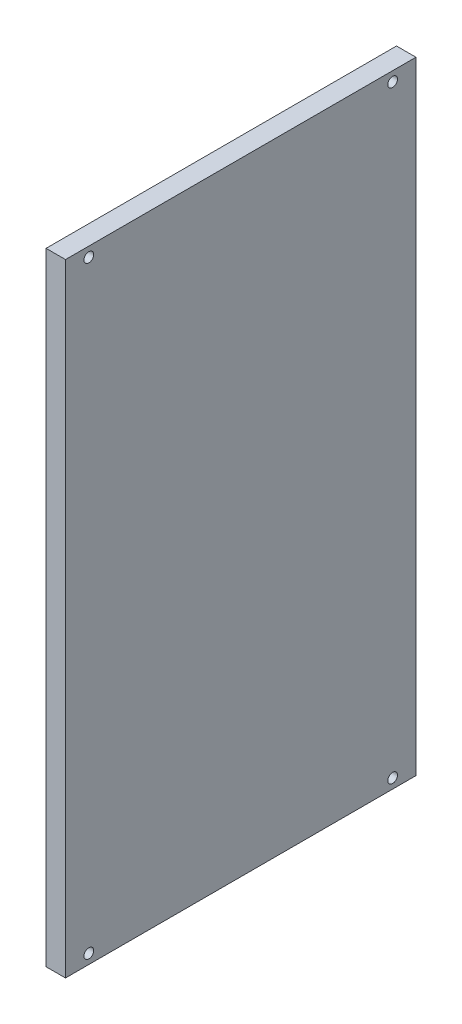
SolidWorks part; units mm, degrees
ref_plane "Front Plane" through (0, 0, 0) normal (0, 0, 1) x (1, 0, 0)
ref_plane "Top Plane" through (0, 0, 0) normal (0, 1, 0) x (1, 0, 0)
ref_plane "Right Plane" through (0, 0, 0) normal (1, 0, 0) x (0, 0, -1)
sketch "Sketch1" plane through (0, 0, 0) normal (1, 0, 0) x (0, 0, -1)
  line L0 (0, 160.065) -> (0, -160.065) construction
  line L1 (-90.15, 160.065) -> (-90.15, -160.065)
  line L2 (-90.15, -160.065) -> (90.15, -160.065)
  line L3 (90.15, -160.065) -> (90.15, 160.065)
  line L4 (90.15, 160.065) -> (-90.15, 160.065)
  line L5 (-90.15, 0) -> (90.15, 0) construction
  circle A0 centre (-78.15, 155.065) radius 2.5
  circle A1 centre (78.15, 155.065) radius 2.5
  circle A2 centre (-78.15, -155.065) radius 2.5
  circle A3 centre (78.15, -155.065) radius 2.5
  dimension "D3" = 5
  dimension "D4" = 5
  dimension "D5" = 12
  dimension "D6" = 5
  dimension "D7" = 5
  dimension "D8" = 12
  dimension "D9" = 5
  dimension "D10" = 12
  dimension "D11" = 5
  dimension "D12" = 5
  dimension "D13" = 12
  dimension "D14" = 5
  dimension "D1" = 320.13
  dimension "D2" = 180.3
extrude "Boss-Extrude1" add sketch "Sketch1" along normal blind 10
